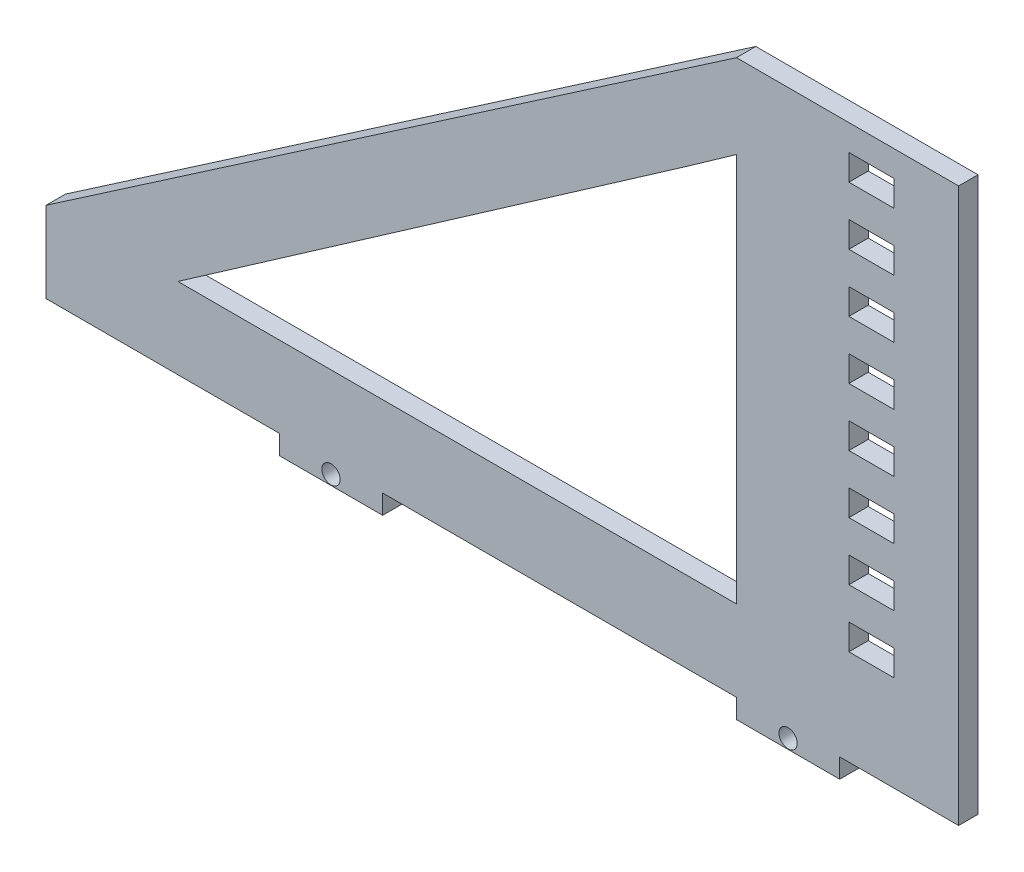
SolidWorks part; units mm, degrees
ref_plane "Front Plane" through (0, 0, 0) normal (0, 0, 1) x (1, 0, 0)
ref_plane "Top Plane" through (0, 0, 0) normal (0, 1, 0) x (1, 0, 0)
ref_plane "Right Plane" through (0, 0, 0) normal (1, 0, 0) x (0, 0, -1)
sketch "Sketch1" plane through (0, 0, 0) normal (0, 0, 1) x (1, 0, 0)
  line L0 (36.1494, 0) -> (36.1494, -3)
  line L1 (0, 0) -> (36.1494, 0)
  line L2 (0, 0) -> (0, 12.5201)
  line L3 (122.9594, 85.8065) -> (106.9594, 85.8065)
  line L4 (141.38, 0) -> (141.38, 27.1055)
  line L5 (122.9594, 0) -> (122.9594, -3)
  line L6 (106.9594, -3) -> (122.9594, -3)
  line L7 (52.1494, 0) -> (106.9594, 0)
  line L8 (36.1494, -3) -> (52.1494, -3)
  line L9 (52.1494, 0) -> (52.1494, -3)
  line L10 (106.9594, 0) -> (106.9594, -3)
  line L11 (122.9594, 0) -> (141.38, 0)
  line L12 (0, 12.5201) -> (106.9594, 85.8065)
  line L13 (122.9594, 85.8065) -> (140.1708, 85.8065)
  line L15 (20.4332, 12.5201) -> (99.1287, 67.2784)
  line L16 (20.4332, 12.5201) -> (99.1287, 12.5201)
  line L18 (124.38, 68.8065) -> (131.38, 68.8065)
  line L19 (124.38, 81.8065) -> (131.38, 81.8065)
  line L20 (141.38, 27.1055) -> (141.38, 85.8065)
  line L21 (141.38, 85.8065) -> (140.1708, 85.8065)
  line L22 (124.38, 81.8065) -> (124.38, 77.8065)
  line L23 (124.38, 77.8065) -> (131.38, 77.8065)
  line L24 (131.38, 81.8065) -> (131.38, 77.8065)
  line L25 (124.38, 72.8065) -> (124.38, 68.8065)
  line L26 (124.38, 72.8065) -> (131.38, 72.8065)
  line L27 (131.38, 72.8065) -> (131.38, 68.8065)
  line L28 (124.38, 59.8065) -> (131.38, 59.8065)
  line L29 (124.38, 63.8065) -> (124.38, 59.8065)
  line L30 (124.38, 63.8065) -> (131.38, 63.8065)
  line L31 (131.38, 63.8065) -> (131.38, 59.8065)
  line L32 (124.38, 50.8065) -> (131.38, 50.8065)
  line L33 (124.38, 54.8065) -> (124.38, 50.8065)
  line L34 (124.38, 54.8065) -> (131.38, 54.8065)
  line L35 (131.38, 54.8065) -> (131.38, 50.8065)
  line L36 (124.38, 41.8065) -> (131.38, 41.8065)
  line L37 (124.38, 45.8065) -> (124.38, 41.8065)
  line L38 (124.38, 45.8065) -> (131.38, 45.8065)
  line L39 (131.38, 45.8065) -> (131.38, 41.8065)
  line L40 (124.38, 32.8065) -> (131.38, 32.8065)
  line L41 (124.38, 36.8065) -> (124.38, 32.8065)
  line L42 (124.38, 36.8065) -> (131.38, 36.8065)
  line L43 (131.38, 36.8065) -> (131.38, 32.8065)
  line L44 (124.38, 23.8065) -> (131.38, 23.8065)
  line L45 (124.38, 27.8065) -> (124.38, 23.8065)
  line L46 (124.38, 27.8065) -> (131.38, 27.8065)
  line L47 (131.38, 27.8065) -> (131.38, 23.8065)
  line L48 (124.38, 14.8065) -> (131.38, 14.8065)
  line L49 (124.38, 18.8065) -> (124.38, 14.8065)
  line L50 (124.38, 18.8065) -> (131.38, 18.8065)
  line L51 (131.38, 18.8065) -> (131.38, 14.8065)
  line L52 (99.1287, 67.2784) -> (106.9594, 72.8065)
  line L53 (106.9594, 72.8065) -> (106.9594, 12.5201)
  line L54 (106.9594, 12.5201) -> (99.1287, 12.5201)
  line L56 (122.9594, 0) -> (122.9594, -3) [skipped]
  line L57 (106.9594, 0) -> (106.9594, -3) [skipped]
  circle A0 centre (44.1494, -1.5) radius 1.42
  circle A1 centre (114.9594, -1.5) radius 1.42
  point P11 (44.1494, -3)
  dimension "D4" = 2.84
  dimension "D1" = 141.38
  dimension "D2" = 3
  dimension "D3" = 2
  dimension "D5" = 1.5
  dimension "D6" = 12.5201
  dimension "D7" = 4
  dimension "D8" = 4
  dimension "D9" = 7
  dimension "D10" = 10
  dimension "D11" = 8
extrude "Boss-Extrude2" add sketch "Sketch1" along normal blind 3
